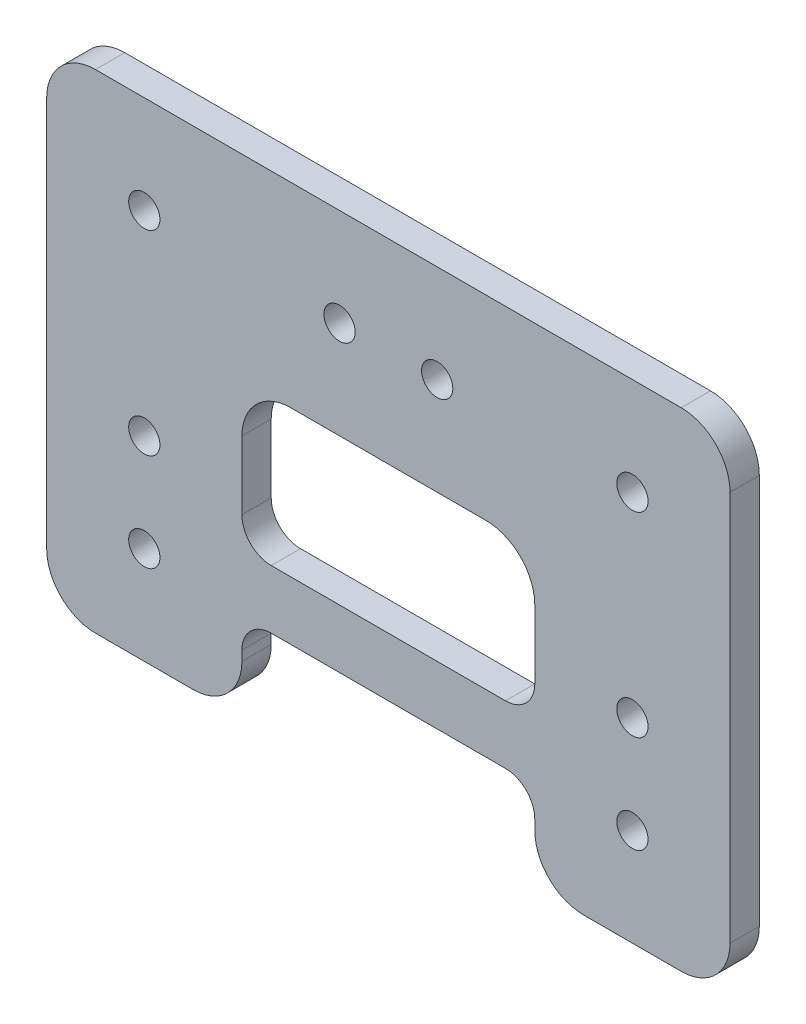
SolidWorks part; units mm, degrees
material "A-玻璃纤维"
ref_plane "前视基准面" through (0, 0, 0) normal (0, 0, 1) x (1, 0, 0)
ref_plane "上视基准面" through (0, 0, 0) normal (0, 1, 0) x (1, 0, 0)
ref_plane "右视基准面" through (0, 0, 0) normal (1, 0, 0) x (0, 0, -1)
sketch "草图1" plane through (0, 0, 0) normal (0, 0, 1) x (1, 0, 0)
  line L0 (0, 21.7727) -> (0, -26.987) construction
  line L1 (-35, 25) -> (35, 25)
  line L2 (-35, 25) -> (-35, -25)
  line L3 (-35, -25) -> (35, -25)
  line L4 (35, 25) -> (35, -25)
  line L5 (-35, 25) -> (35, -25) construction
  line L6 (-35, -25) -> (35, 25) construction
  circle A0 centre (-25, -15) radius 1.6
  circle A1 centre (-25, -5) radius 1.6
  circle A2 centre (-25, 15) radius 1.6
  circle A3 centre (-5, 15) radius 1.6
  circle A8 centre (5, 15) radius 1.6
  circle A9 centre (25, 15) radius 1.6
  circle A10 centre (25, -5) radius 1.6
  circle A11 centre (25, -15) radius 1.6
  point P0 (0, 0)
  dimension "D1" = 10
  dimension "D2" = 20
  dimension "D3" = 20
  dimension "D4" = 10
  dimension "D5" = 10
  dimension "D6" = 3.2
  dimension "D7" = 10
  dimension "D8" = 10
extrude "凸台-拉伸1" add sketch "草图1" along normal blind 3
sketch "草图2" plane through (0, 0, 3) normal (0, 0, 1) x (1, 0, 0)
  line L0 (0, 37.1728) -> (0, -37.8319) construction
  line L1 (-15, -25) -> (-15, 5)
  line L2 (-35, -25) -> (35, -25) construction
  line L3 (-15, 5) -> (15, 5)
  line L4 (15, 5) -> (15, -25)
  line L5 (15, -25) -> (-15, -25)
  circle A0 centre (25, -15) radius 1.6 construction
  circle A1 centre (5, 15) radius 1.6 construction
  dimension "D1" = 10
  dimension "D2" = 10
extrude "切除-拉伸1" cut sketch "草图2" against normal through all
fillet "圆角1" radius 5 8 edges at (-35, 25, 1.5) (35, 25, 1.5) (35, -25, 1.5) (15, -25, 1.5) (-35, -25, 1.5) (-15, -25, 1.5) (15, 5, 1.5) (-15, 5, 1.5)
sketch "草图3" plane through (0, 0, 3) normal (0, 0, 1) x (1, 0, 0)
  line L0 (-15, -16) -> (15, -16)
  line L1 (-15, 0) -> (-15, -20) construction
  line L2 (15, -20) -> (15, 0) construction
  line L3 (15, -16) -> (15, -10)
  line L4 (15, -10) -> (-15, -10)
  line L5 (-15, -10) -> (-15, -16)
  line L6 (42.1053, 0) -> (-43.3945, 0) construction
  dimension "D1" = 10
  dimension "D2" = 6
extrude "凸台-拉伸2" add sketch "草图3" against normal blind 3
fillet "圆角2" radius 3 4 edges at (15, -10, 1.5) (15, -16, 1.5) (-15, -16, 1.5) (-15, -10, 1.5)
